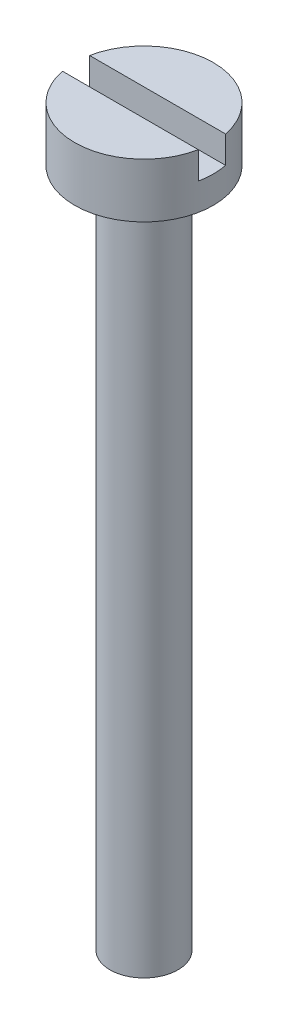
SolidWorks part; units mm, degrees
material "1023 Carbon Steel Sheet (SS)"
ref_plane "Front Plane" through (0, 0, 0) normal (0, 0, 1) x (1, 0, 0)
ref_plane "Top Plane" through (0, 0, 0) normal (0, 1, 0) x (1, 0, 0)
ref_plane "Right Plane" through (0, 0, 0) normal (1, 0, 0) x (0, 0, -1)
sketch "Sketch1" plane through (0, 0, 0) normal (0, 1, 0) x (1, 0, 0)
  circle A0 centre (0, 0) radius 2.55
  dimension "D1" = 5.1
extrude "Boss-Extrude1" add sketch "Sketch1" along normal blind 2
sketch "Sketch2" plane through (0, 0, 0) normal (0, 1, 0) x (1, 0, 0)
  circle A0 centre (0, 0) radius 1.25
  dimension "D1" = 2.5
extrude "Boss-Extrude2" add sketch "Sketch2" against normal blind 25
sketch "Sketch3" plane through (0, 2, 0) normal (0, 1, 0) x (1, 0, 0)
  line L1 (-3, -0.5) -> (3, -0.5)
  line L2 (-3, -0.5) -> (-3, 0.5)
  line L3 (-3, 0.5) -> (3, 0.5)
  line L4 (3, -0.5) -> (3, 0.5)
  line L5 (-3, -0.5) -> (3, 0.5) construction
  line L6 (-3, 0.5) -> (3, -0.5) construction
  point P0 (0, 0)
  dimension "D1" = 1
  dimension "D2" = 6
extrude "Cut-Extrude1" cut sketch "Sketch3" against normal blind 1
